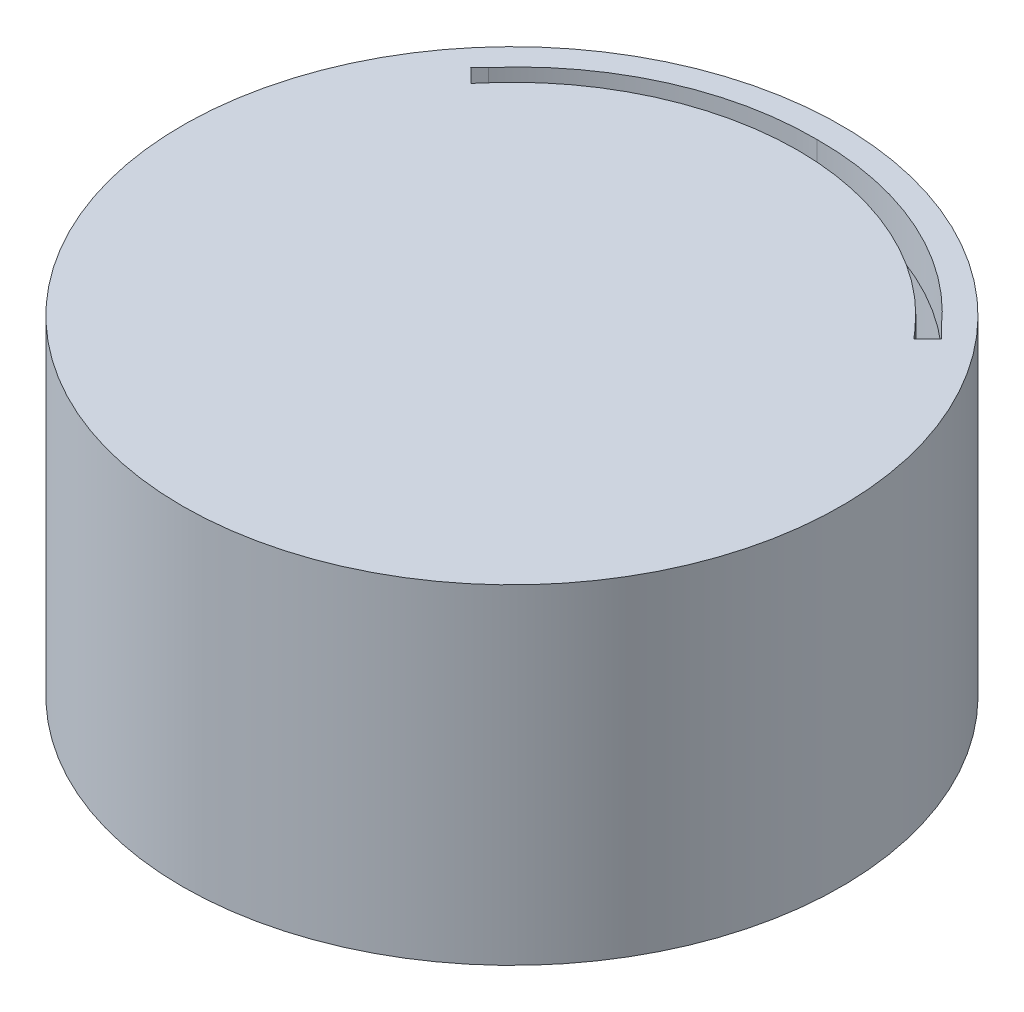
SolidWorks part; units mm, degrees
ref_plane "前基準面" through (0, 0, 0) normal (0, 0, 1) x (1, 0, 0)
ref_plane "上基準面" through (0, 0, 0) normal (0, 1, 0) x (1, 0, 0)
ref_plane "右基準面" through (0, 0, 0) normal (1, 0, 0) x (0, 0, -1)
sketch "草圖1" plane through (0, 0, 0) normal (0, 1, 0) x (1, 0, 0)
  circle A0 centre (0, 0) radius 30
  dimension "D1" = 60
extrude "填料-伸長1" add sketch "草圖1" along normal blind 30
sketch "草圖2" plane through (0, 0, 0) normal (0, 1, 0) x (1, 0, 0)
  circle A0 centre (0, 0) radius 29
  dimension "D1" = 58
extrude "除料-伸長1" cut sketch "草圖2" along normal blind 26
sketch "草圖4" plane through (0, 0, 0) normal (0, 1, 0) x (1, 0, 0)
  line L5 (-0.0254, -0.131) -> (-0.0254, 26.0645) construction
  line L6 (-0.0254, 27.7828) -> (-0.0254, 27.5)
  line L8 (-0.0254, 27.5) -> (-0.0254, 30.7023) construction
  line L9 (-20.6221, 18.5104) -> (-21.441, 17.6914)
  line L10 (-19.5513, 17.1756) -> (-20.1753, 16.4556)
  line L11 (-20.1753, 16.4556) -> (-21.441, 17.6914)
  line L12 (20.5713, 18.5104) -> (21.3902, 17.6914)
  line L13 (20.1245, 16.4556) -> (21.3902, 17.6914)
  line L14 (19.5005, 17.1756) -> (20.1245, 16.4556)
  arc A6 (-20.6221, 18.5104) -> (-0.0254, 27.7828) centre (-0.2695, 0.8132) cw
  arc A7 (-19.5513, 17.1756) -> (-0.0254, 26.0645) centre (0.0146, 0.0865) cw
  arc A8 (20.5713, 18.5104) -> (-0.0254, 27.7828) centre (0.2187, 0.8132) ccw
  arc A9 (19.5005, 17.1756) -> (-0.0254, 26.0645) centre (-0.0654, 0.0865) ccw
extrude "除料-伸長3" cut sketch "草圖4" along normal blind 74 contours A8 L12 L13 L14 A9 A7 L10 L11 L9 A6
